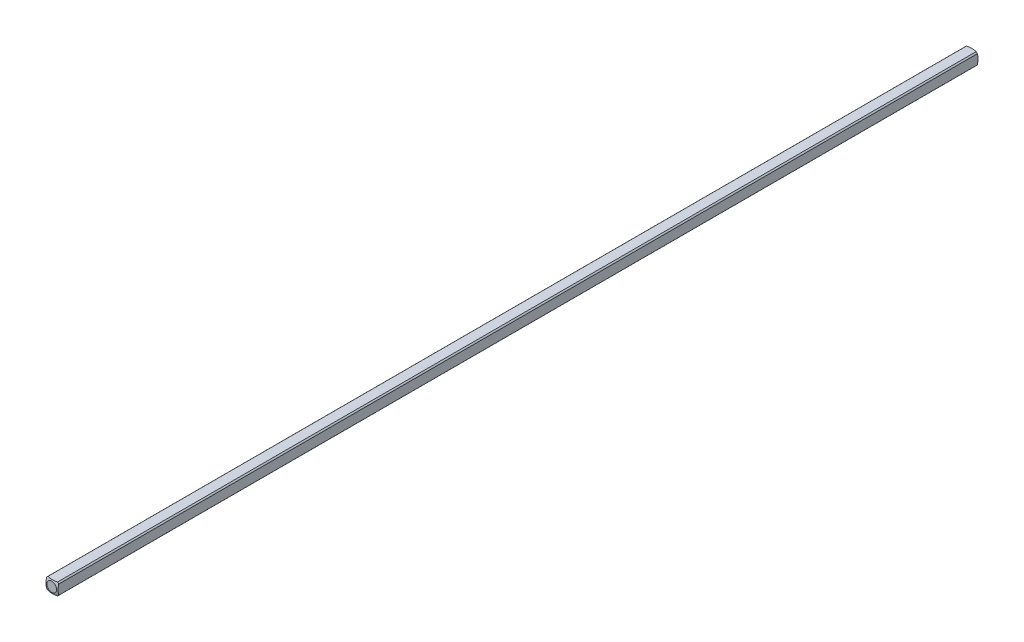
SolidWorks part; units mm, degrees
material "Custom Plastic"
ref_plane "Front Plane" through (0, 0, 0) normal (0, 0, 1) x (1, 0, 0)
ref_plane "Top Plane" through (0, 0, 0) normal (0, 1, 0) x (1, 0, 0)
ref_plane "Right Plane" through (0, 0, 0) normal (1, 0, 0) x (0, 0, -1)
sketch "Sketch1" plane through (0, 0, 0) normal (0, 0, 1) x (1, 0, 0)
  line L0 (-1.5875, -1.5875) -> (1.5875, 1.5875) construction
  line L1 (-1.5875, -1.5875) -> (1.5875, -1.5875)
  line L2 (-1.5875, -1.5875) -> (-1.5875, 1.5875)
  line L3 (-1.5875, 1.5875) -> (1.5875, 1.5875)
  line L4 (1.5875, -1.5875) -> (1.5875, 1.5875)
  dimension "D1" = 3.175
extrude "Boss-Extrude1" add sketch "Sketch1" along normal blind 120.65
sketch "Sketch2" plane through (0, 0, 0) normal (0, 0, -1) x (-1, 0, 0)
  circle A0 centre (0, 0) radius 2.032
  dimension "D1" = 4.064
extrude "Cut-Extrude1" cut sketch "Sketch2" against normal through all flip side to cut
ref_axis "Axis1" through (0, 0, 120.65) along (0, 0, -1)
sketch "Sketch3" plane through (0, 0, 0) normal (0, 1, 0) x (1, 0, 0)
  line L1 (-5.0537, -4.4027) -> (-5.0537, 5.7405)
  line L2 (-5.0537, 5.7405) -> (0, 5.7405)
  line L5 (0, -120.65) -> (0, 0) construction
  line L8 (0, 0.1609) -> (0, 5.7405)
  arc A0 (-5.0537, -4.4027) -> (0, 0.1609) centre (0, -4.9191) cw
  dimension "D1" = 5.08
revolve "Cut-Revolve1" cut sketch "Sketch3" angle 360 about axis through (0, 0, 120.65) along (0, 0, -1)
mirror "Mirror1" about plane through (0, 0, 120.65) normal (0, 0, -1) of bodies 103
